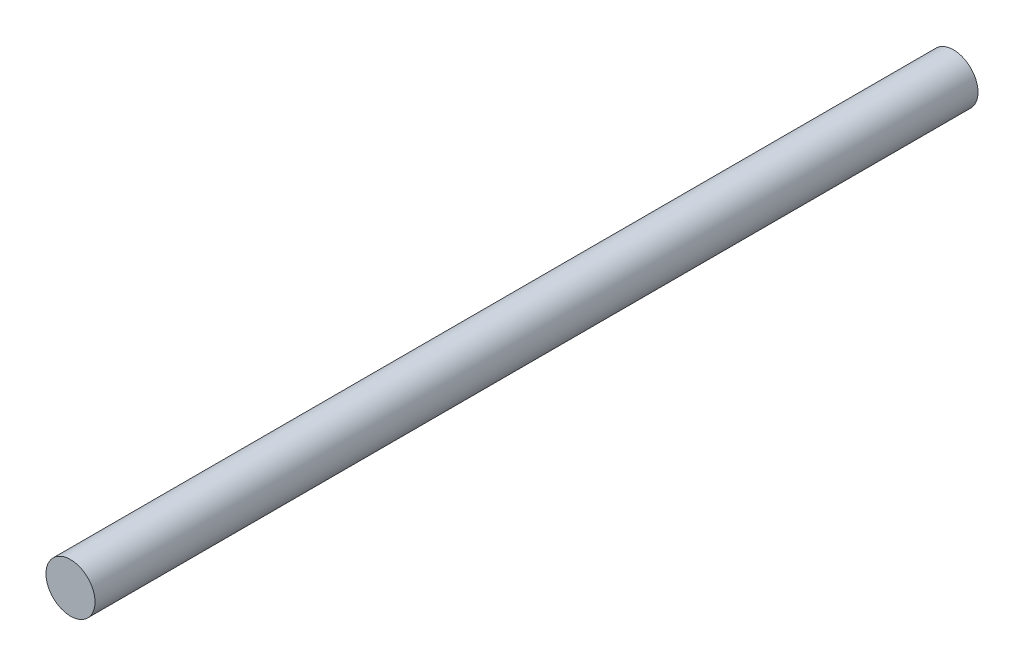
SolidWorks part; units mm, degrees
ref_plane "Front Plane" through (0, 0, 0) normal (0, 0, 1) x (1, 0, 0)
ref_plane "Top Plane" through (0, 0, 0) normal (0, 1, 0) x (1, 0, 0)
ref_plane "Right Plane" through (0, 0, 0) normal (1, 0, 0) x (0, 0, -1)
sketch "Sketch1" plane through (0, 0, 0) normal (0, 0, 1) x (1, 0, 0)
  circle A0 centre (0, 0) radius 10
  dimension "D1" = 20
extrude "Boss-Extrude1" add sketch "Sketch1" along normal mid plane 360
